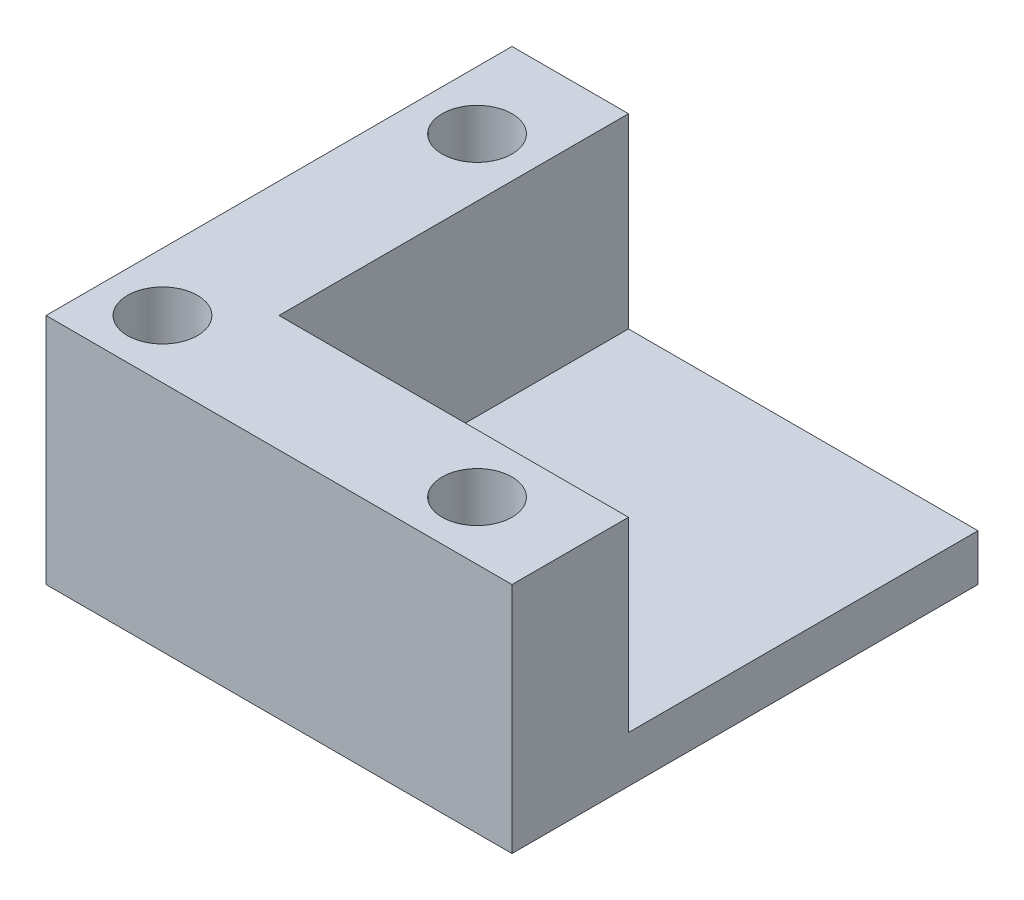
SolidWorks part; units mm, degrees
ref_plane "Front Plane" through (0, 0, 0) normal (0, 0, 1) x (1, 0, 0)
ref_plane "Top Plane" through (0, 0, 0) normal (0, 1, 0) x (1, 0, 0)
ref_plane "Right Plane" through (0, 0, 0) normal (1, 0, 0) x (0, 0, -1)
sketch "Sketch1" plane through (0, 0, 0) normal (0, 1, 0) x (1, 0, 0)
  line L1 (0, 0) -> (25.4, 0)
  line L2 (0, 0) -> (0, 25.4)
  line L3 (0, 25.4) -> (25.4, 25.4)
  line L4 (25.4, 0) -> (25.4, 25.4)
  dimension "D1" = 25.4
  dimension "D2" = 25.4
extrude "Boss-Extrude1" add sketch "Sketch1" along normal blind 2.54
sketch "Sketch2" plane through (0, 2.54, 0) normal (0, 1, 0) x (1, 0, 0)
  line L0 (0, 25.4) -> (0, 0)
  line L1 (0, 0) -> (25.4, 0)
  line L2 (25.4, 0) -> (25.4, 6.35)
  line L3 (25.4, 0) -> (25.4, 25.4) construction
  line L4 (0, 25.4) -> (6.35, 25.4)
  line L5 (25.4, 25.4) -> (0, 25.4) construction
  line L6 (6.35, 25.4) -> (6.35, 6.35)
  line L7 (6.35, 6.35) -> (25.4, 6.35)
  dimension "D1" = 6.35
  dimension "D2" = 6.35
extrude "Boss-Extrude2" add sketch "Sketch2" along normal blind 10.16
sketch "Sketch3" plane through (0, 12.7, 0) normal (0, 1, 0) x (1, 0, 0)
  line L0 (3.175, 25.4) -> (3.175, 0) construction
  line L1 (6.35, 25.4) -> (0, 25.4) construction
  line L2 (0, 0) -> (25.4, 0) construction
  line L3 (25.4, 3.175) -> (3.175, 3.175) construction
  line L4 (25.4, 0) -> (25.4, 6.35) construction
  circle A0 centre (3.175, 20.32) radius 1.905
  circle A1 centre (3.175, 3.175) radius 1.905
  circle A2 centre (20.32, 3.175) radius 1.905
  dimension "D1" = 3.81
  dimension "D2" = 5.08
  dimension "D3" = 3.81
  dimension "D4" = 3.81
  dimension "D5" = 5.08
extrude "Cut-Extrude1" cut sketch "Sketch3" against normal blind 6.35
